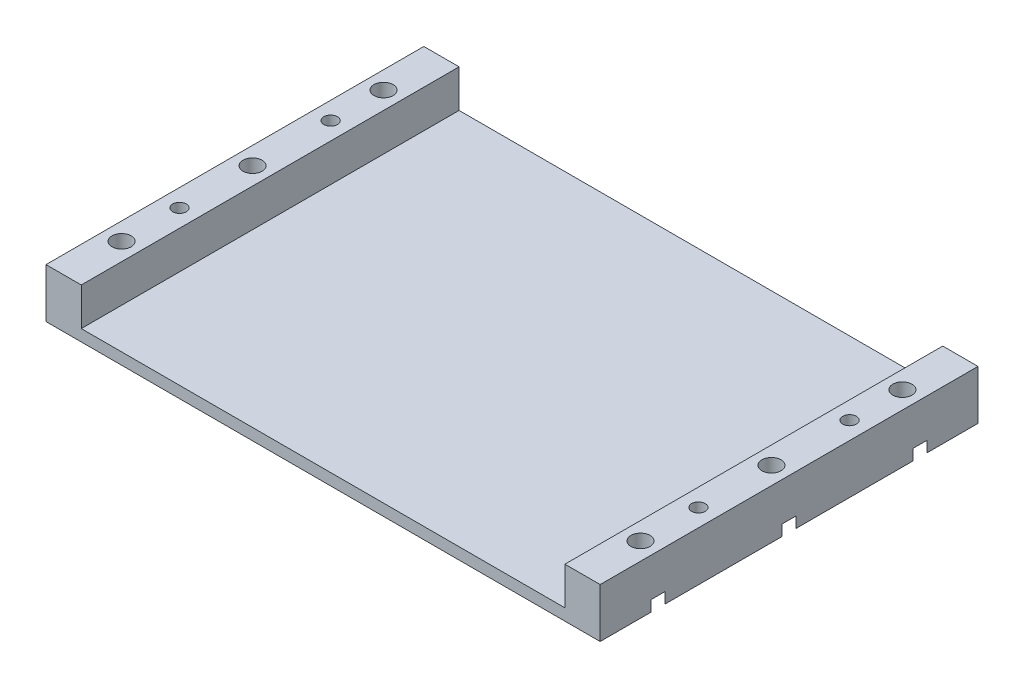
SolidWorks part; units mm, degrees
ref_plane "Front Plane" through (0, 0, 0) normal (0, 0, 1) x (1, 0, 0)
ref_plane "Top Plane" through (0, 0, 0) normal (0, 1, 0) x (1, 0, 0)
ref_plane "Right Plane" through (0, 0, 0) normal (1, 0, 0) x (0, 0, -1)
sketch "Sketch1" plane through (0, 0, 0) normal (0, 1, 0) x (1, 0, 0)
  line L0 (0, 73.5868) -> (1.4132, 75) construction
  line L1 (0, 0) -> (96, 0)
  line L2 (0, 0) -> (0, 75)
  line L3 (0, 75) -> (96, 75)
  line L4 (96, 0) -> (96, 75)
  line L5 (1.4132, 75) -> (94.5868, 75)
  line L6 (94.5868, 75) -> (96, 73.5868) construction
  line L7 (96, 73.5868) -> (96, 1.4132)
  line L8 (96, 1.4132) -> (94.5868, 0) construction
  line L9 (94.5868, 0) -> (1.4132, 0)
  line L10 (1.4132, 0) -> (0, 1.4132) construction
  line L11 (0, 1.4132) -> (0, 73.5868)
  dimension "D1" = 96
  dimension "D2" = 75
extrude "Boss-Extrude1" add sketch "Sketch1" along normal blind 2.3 contours L1 L4 L3 L2
ref_plane "center-of-slot" [suppressed] through (0, 1.143, 0) normal (0, 1, 0) x (1, 0, 0)
sketch "Sketch2" plane through (0, 2.3, 0) normal (0, 1, 0) x (1, 0, 0)
  line L0 (0, 0) -> (96, 0) construction
  line L1 (0, 75) -> (-7, 75)
  line L2 (0, 75) -> (0, 0)
  line L3 (0, 0) -> (-7, 0)
  line L4 (-7, 75) -> (-7, 0)
  dimension "D1" = 7
extrude "Boss-Extrude2" add sketch "Sketch2" along normal blind 7.5 and the other way up to surface (2.3 mm away) other way up to face at (48, 0, -37.5)
sketch "Sketch3" plane through (0, 2.3, 0) normal (0, 1, 0) x (1, 0, 0)
  line L0 (0, 0) -> (96, 0) construction
  line L1 (96, 75) -> (103, 75)
  line L2 (96, 75) -> (96, 0)
  line L3 (96, 0) -> (103, 0)
  line L4 (103, 75) -> (103, 0)
  line L5 (0, 75) -> (-7, 75) construction
extrude "Boss-Extrude3" add sketch "Sketch3" along normal up to surface and the other way up to surface up to face at (-3.5, 9.8, -37.5) other way up to face at (44.5, 0, -37.5)
hole_wizard "#6-32 Tapped Hole1" positions "Sketch5" profile "Sketch4" tap size "#6-32" standard "ANSI Inch" end condition through all
sketch "Sketch5" plane through (0, 0, 0) normal (0, -1, 0) x (-1, 0, 0)
  line L0 (-103, 75) -> (-103, 0) construction
  line L2 (7, 0) -> (-103, 0) construction
  line L3 (7, 75) -> (-103, 75) construction
  line L4 (7, 0) -> (7, 75) construction
  point P11 (-99.5, 23)
  point P13 (-99.5, 53)
  point P30 (3.5, 23)
  point P32 (3.5, 53)
  dimension "D1" = 3.5
  dimension "D2" = 23
  dimension "D3" = 22
  dimension "D4" = 3.5
sketch "Sketch4" plane through (99.5, 0, -23) normal (1, 0, 0) x (0, 0, -1)
  line L0 (0, 0) -> (0, 9.8)
  line L1 (0, 9.8) -> (1.3525, 9.8)
  line L3 (1.3525, 9.8) -> (1.3525, 7.01)
  line L4 (1.3525, 7.01) -> (1.7526, 7.01)
  line L5 (1.7526, 7.01) -> (1.7526, 0)
  line L7 (1.7526, 0) -> (0, 0)
  line L11 (0, -6.35) -> (0, 107.95) construction
  dimension "Thru Tap Drill Dia." = 2.7051
  dimension "Thru Tap Drill Depth" = 9.8
  dimension "Thread Major Dia." = 3.5052
  dimension "Thread Depth" = 7.01
hole_wizard "CBORE for #6 Button Head Cap Screw1" positions "Sketch7" profile "Sketch6" counterbore size "#6" standard "ANSI Inch" end condition through all
sketch "Sketch7" plane through (0, 0, 0) normal (0, -1, 0) x (-1, 0, 0)
  line L0 (-99.5, 63.5) -> (-99.5, 37.5) construction
  line L1 (-99.5, 37.5) -> (-99.5, 11.5) construction
  line L2 (-99.5, 11.5) -> (3.5, 11.5) construction
  line L3 (3.5, 11.5) -> (3.5, 37.5) construction
  line L4 (3.5, 37.5) -> (3.5, 63.5) construction
  line L6 (-99.5, 37.5) -> (-103, 37.5) construction
  line L7 (-103, 75) -> (-103, 0) construction
  line L9 (-99.5, 11.5) -> (-99.5, 23) construction
  line L11 (3.5, 11.5) -> (3.5, 23) construction
  circle A3 centre (-99.5, 23) radius 1.7526 construction
  point P0 (-99.5, 63.5)
  point P2 (-99.5, 37.5)
  point P4 (-99.5, 11.5)
  point P6 (3.5, 11.5)
  point P8 (3.5, 37.5)
  point P10 (3.5, 63.5)
  dimension "D1" = 26
sketch "Sketch6" plane through (99.5, 0, -63.5) normal (1, 0, 0) x (0, 0, -1)
  line L0 (0, 0) -> (0, 9.8)
  line L1 (0, 9.8) -> (1.8986, 9.8)
  line L3 (1.8986, 9.8) -> (1.8986, 2.1542)
  line L4 (1.8986, 2.1542) -> (3.7706, 2.1542)
  line L5 (3.7706, 2.1542) -> (3.7706, 0)
  line L7 (3.7706, 0) -> (0, 0)
  line L11 (0, -6.35) -> (0, 107.95) construction
  dimension "Thru Hole Dia." = 3.7973
  dimension "Thru Hole Depth" = 9.8
  dimension "C'Bore Dia." = 7.5413
  dimension "C'Bore Depth" = 2.1542
